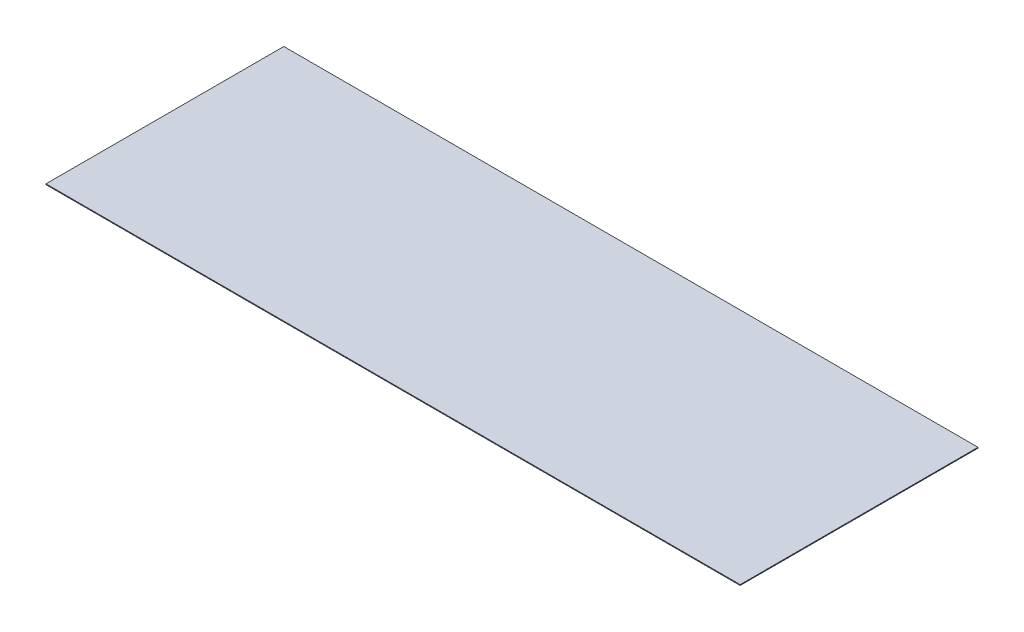
SolidWorks part; units mm, degrees
ref_plane "Front Plane" through (0, 0, 0) normal (0, 0, 1) x (1, 0, 0)
ref_plane "Top Plane" through (0, 0, 0) normal (0, 1, 0) x (1, 0, 0)
ref_plane "Right Plane" through (0, 0, 0) normal (1, 0, 0) x (0, 0, -1)
sketch "Sketch1" plane through (0, 0, 0) normal (0, 1, 0) x (1, 0, 0)
  line L1 (-437.843, 150) -> (437.843, 150)
  line L2 (-437.843, 150) -> (-437.843, -150)
  line L3 (-437.843, -150) -> (437.843, -150)
  line L4 (437.843, 150) -> (437.843, -150)
  line L5 (-437.843, 150) -> (437.843, -150) construction
  line L6 (-437.843, -150) -> (437.843, 150) construction
  point P0 (0, 0)
extrude "Boss-Extrude1" add sketch "Sketch1" along normal blind 1
